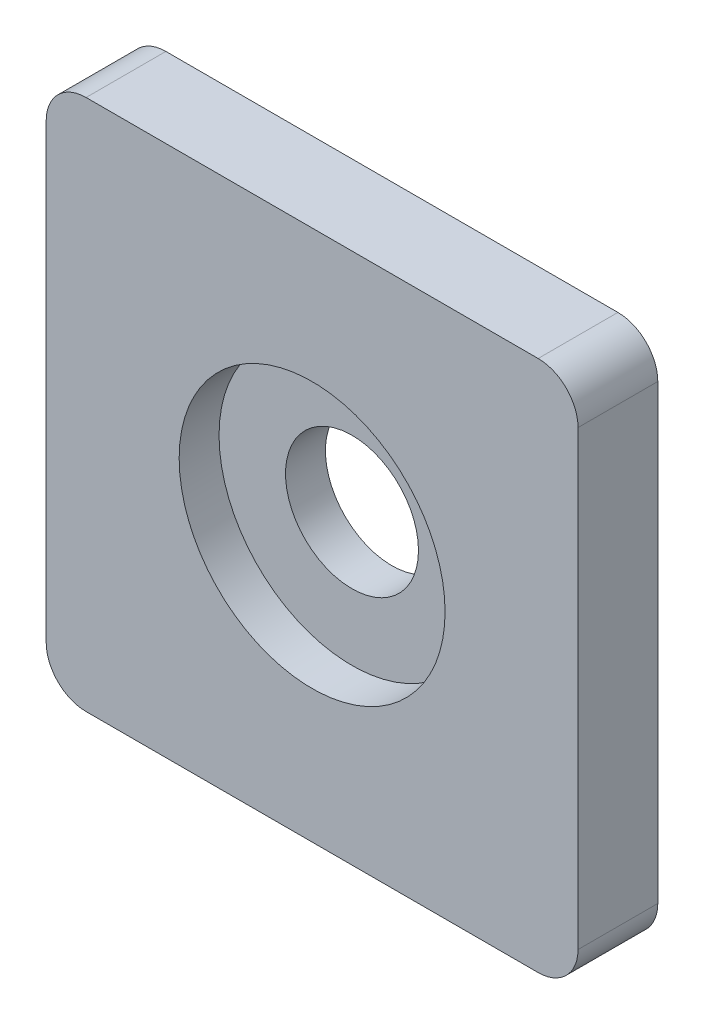
SolidWorks part; units mm, degrees
material "6061-T6 (SS)"
ref_plane "Front Plane" through (0, 0, 0) normal (0, 0, 1) x (1, 0, 0)
ref_plane "Top Plane" through (0, 0, 0) normal (0, 1, 0) x (1, 0, 0)
ref_plane "Right Plane" through (0, 0, 0) normal (1, 0, 0) x (0, 0, -1)
sketch "Sketch1" plane through (0, 0, 0) normal (0, 0, 1) x (1, 0, 0)
  line L1 (10, -10) -> (-10, -10)
  line L2 (10, -10) -> (10, 10)
  line L3 (10, 10) -> (-10, 10)
  line L4 (-10, -10) -> (-10, 10)
  line L5 (10, -10) -> (-10, 10) construction
  line L6 (10, 10) -> (-10, -10) construction
  circle A0 centre (0, 0) radius 2.5
  point P0 (0, 0)
  dimension "D2" = 5
  dimension "D1" = 20
extrude "Boss-Extrude1" add sketch "Sketch1" along normal blind 3
sketch "Sketch2" plane through (0, 0, 3) normal (0, 0, 1) x (1, 0, 0)
  circle A0 centre (0, 0) radius 5
  dimension "D1" = 10
extrude "Cut-Extrude1" cut sketch "Sketch2" against normal blind 1.5
fillet "Fillet1" radius 1.5 4 edges at (10, 10, 1.5) (10, -10, 1.5) (-10, -10, 1.5) (-10, 10, 1.5)
